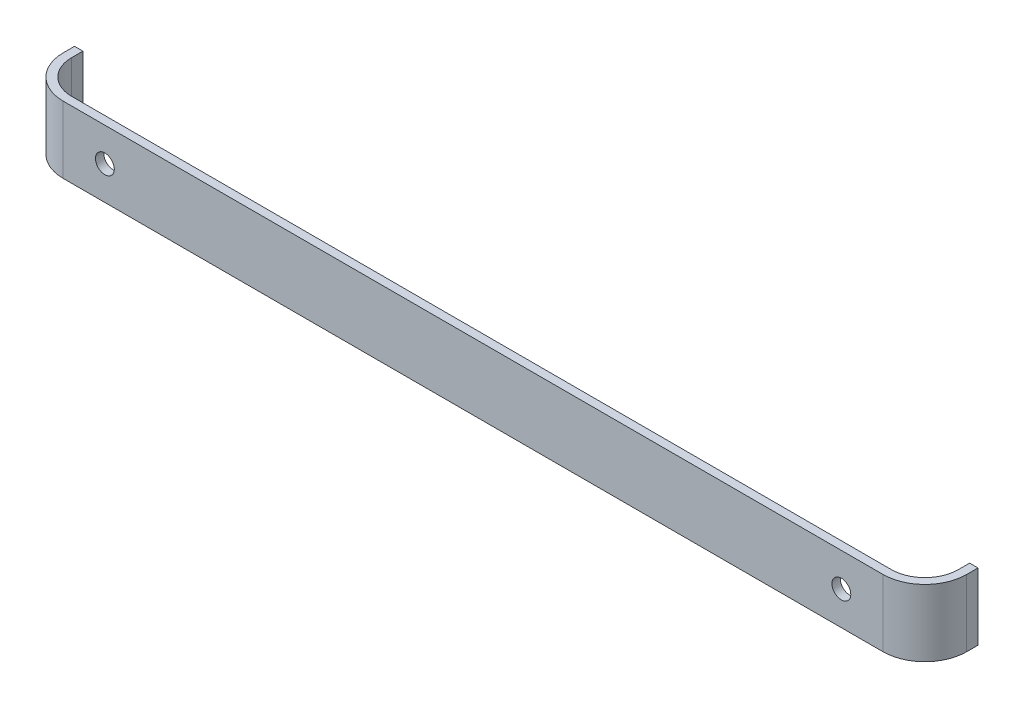
SolidWorks part; units mm, degrees
material "6061-T6 (SS)"
ref_plane "Front Plane" through (0, 0, 0) normal (0, 0, 1) x (1, 0, 0)
ref_plane "Top Plane" through (0, 0, 0) normal (0, 1, 0) x (1, 0, 0)
ref_plane "Right Plane" through (0, 0, 0) normal (1, 0, 0) x (0, 0, -1)
sketch "Sketch1" plane through (0, 0, 0) normal (0, 1, 0) x (1, 0, 0)
  line L0 (0, 0) -> (211.9, 0)
  line L1 (211.9, 0) -> (211.9, 10.7)
  line L2 (211.9, 10.7) -> (213.9, 10.7)
  line L3 (213.9, 10.7) -> (213.9, -2)
  line L4 (213.9, -2) -> (-2, -2)
  line L5 (-2, -2) -> (-2, 10.7)
  line L6 (-2, 10.7) -> (0, 10.7)
  line L7 (0, 10.7) -> (0, 0)
  line L8 (0, 0) -> (0, -2) construction
  dimension "D1" = 2
  dimension "D2" = 215.9
  dimension "D3" = 12.7
extrude "Boss-Extrude1" add sketch "Sketch1" along normal blind 16
fillet "Fillet1" radius 8 2 edges at (211.9, 8, 0) (0, 8, 0)
fillet "Fillet2" radius 10 2 edges at (-2, 8, 2) (213.9, 8, 2)
sketch "Sketch2" plane through (0, 0, 2) normal (0, 0, 1) x (1, 0, 0)
  line L0 (17.95, 8) -> (193.95, 8) construction
  line L1 (105.95, 8) -> (105.95, 16) construction
  line L2 (8, 16) -> (203.9, 16) construction
  line L3 (105.95, 8) -> (105.95, 0) construction
  line L4 (8, 0) -> (203.9, 0) construction
  circle A0 centre (17.95, 8) radius 2.25
  circle A1 centre (193.95, 8) radius 2.25
  dimension "D2" = 4.5
  dimension "D1" = 176
extrude "Cut-Extrude1" cut sketch "Sketch2" against normal through all
